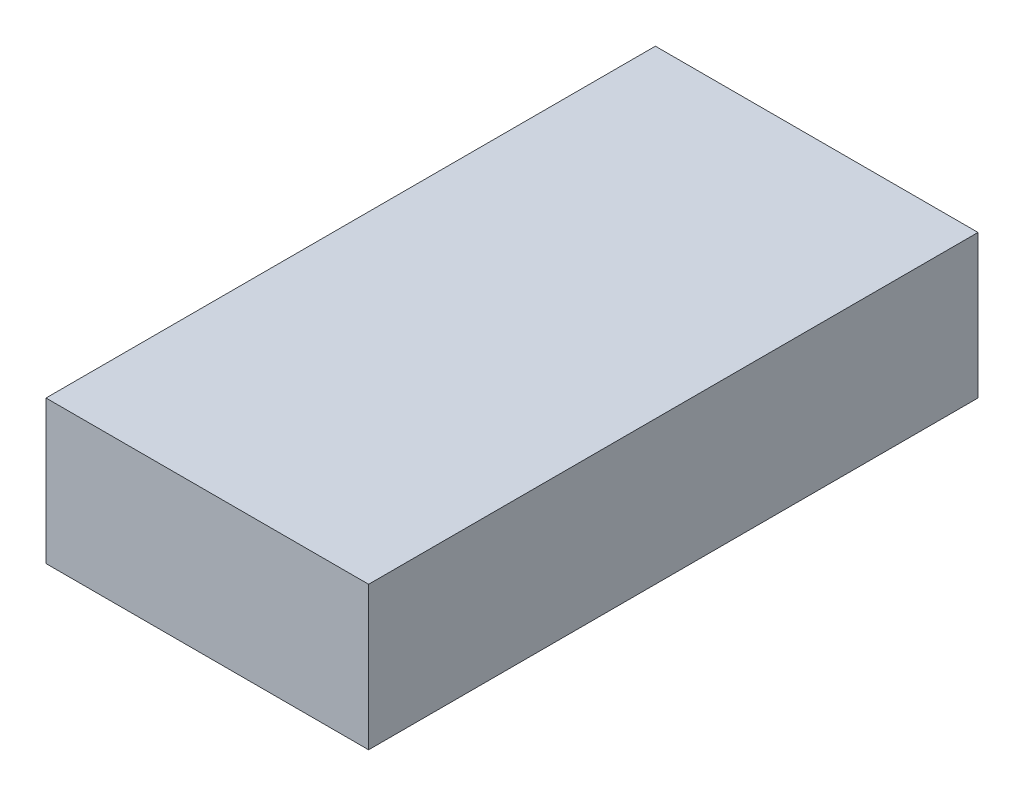
SolidWorks part; units mm, degrees
material "Rhino 2S 1050 mAh "
ref_plane "Front Plane" through (0, 0, 0) normal (0, 0, 1) x (1, 0, 0)
ref_plane "Top Plane" through (0, 0, 0) normal (0, 1, 0) x (1, 0, 0)
ref_plane "Right Plane" through (0, 0, 0) normal (1, 0, 0) x (0, 0, -1)
sketch "Sketch1" plane through (0, 0, 0) normal (0, 1, 0) x (1, 0, 0)
  line L1 (-18, -34) -> (18, -34)
  line L2 (-18, -34) -> (-18, 34)
  line L3 (-18, 34) -> (18, 34)
  line L4 (18, -34) -> (18, 34)
  line L5 (-18, -34) -> (18, 34) construction
  line L6 (-18, 34) -> (18, -34) construction
  point P0 (0, 0)
  dimension "D1" = 68
  dimension "D2" = 36
extrude "Boss-Extrude1" add sketch "Sketch1" along normal blind 16
